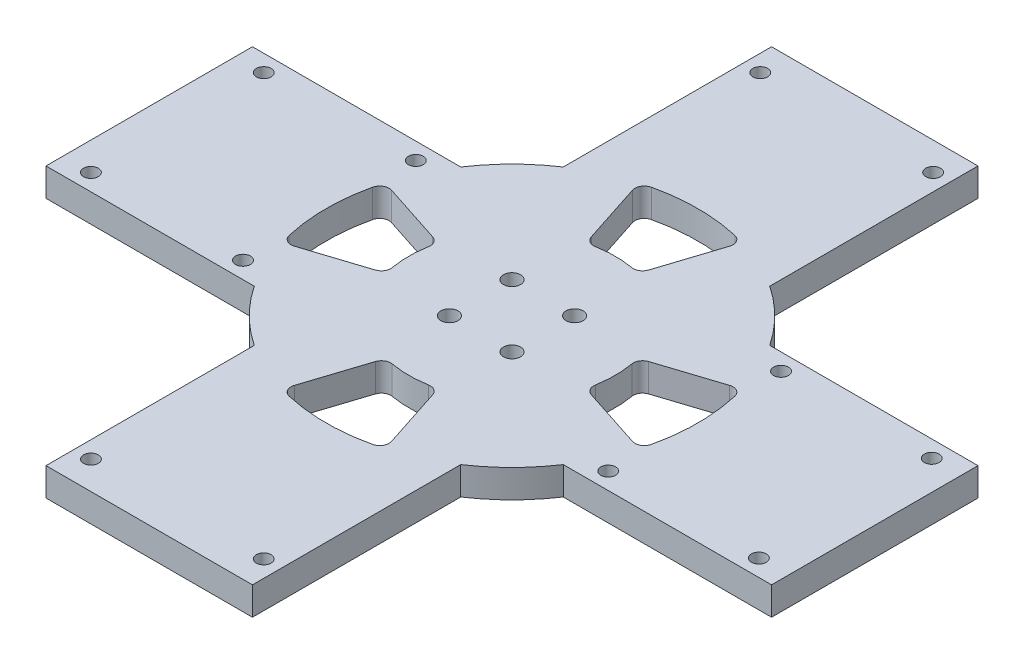
SolidWorks part; units mm, degrees
material "6061-T6 (SS)"
ref_plane "Front" through (0, 0, 0) normal (0, 0, 1) x (1, 0, 0)
ref_plane "Top" through (0, 0, 0) normal (0, 1, 0) x (1, 0, 0)
ref_plane "Right" through (0, 0, 0) normal (1, 0, 0) x (0, 0, -1)
sketch "Sketch1" plane through (0, 0, 0) normal (0, 1, 0) x (1, 0, 0)
  line L0 (0, 0) -> (8.8388, 8.8388) construction
  line L1 (0, 0) -> (-8.8388, -8.8388) construction
  line L2 (0, 0) -> (8.8388, -8.8388) construction
  line L3 (0, 0) -> (-8.8388, 8.8388) construction
  line L4 (-61.5, 17.5) -> (-26.1916, 17.5)
  line L5 (61.5, 17.5) -> (61.5, -17.5)
  line L6 (61.5, -17.5) -> (26.1916, -17.5)
  line L7 (-61.5, -17.5) -> (-61.5, 17.5)
  line L8 (-61.5, 0) -> (61.5, 0) construction
  line L9 (-17.5, 61.5) -> (17.5, 61.5)
  line L10 (-17.5, 61.5) -> (-17.5, 26.1916)
  line L11 (-17.5, -61.5) -> (17.5, -61.5)
  line L12 (17.5, -61.5) -> (17.5, -26.1916)
  line L13 (26.1916, 17.5) -> (61.5, 17.5)
  line L14 (-26.1916, -17.5) -> (-61.5, -17.5)
  line L15 (-17.5, -26.1916) -> (-17.5, -61.5)
  line L16 (17.5, 26.1916) -> (17.5, 61.5)
  line L17 (0, 61.5) -> (0, -61.5) construction
  line L18 (-8.75, 31.5) -> (-8.75, 15.1554) construction
  line L19 (8.75, 31.5) -> (8.75, 15.1554) construction
  line L20 (-31.5, 8.75) -> (-15.1554, 8.75) construction
  line L21 (-31.5, -8.75) -> (-15.1554, -8.75) construction
  line L22 (-8.75, -31.5) -> (-8.75, -15.1554) construction
  line L23 (8.75, -31.5) -> (8.75, -15.1554) construction
  line L24 (31.5, 8.75) -> (15.1554, 8.75) construction
  line L25 (31.5, -8.75) -> (15.1554, -8.75) construction
  line L34 (-4.4194, 4.4194) -> (-16.9328, 4.4194) construction
  line L35 (-4.4194, -4.4194) -> (-16.9328, -4.4194) construction
  line L36 (-4.4194, 4.4194) -> (-4.4194, 16.9328) construction
  line L37 (4.4194, 4.4194) -> (4.4194, 16.9328) construction
  line L38 (4.4194, 4.4194) -> (16.9328, 4.4194) construction
  line L39 (4.4194, -4.4194) -> (16.9328, -4.4194) construction
  line L40 (-4.4194, -4.4194) -> (-4.4194, -16.9328) construction
  line L41 (4.4194, -4.4194) -> (4.4194, -16.9328) construction
  line L42 (-18.3, 4.8637) -> (-28.6574, 8.2292)
  line L43 (-18.3, -4.8637) -> (-28.6574, -8.2292)
  line L44 (-4.8637, 18.3) -> (-8.2292, 28.6574)
  line L45 (4.8637, 18.3) -> (8.2292, 28.6574)
  line L46 (18.3, 4.8637) -> (28.6574, 8.2292)
  line L47 (18.3, -4.8637) -> (28.6574, -8.2292)
  line L48 (4.8637, -18.3) -> (8.2292, -28.6574)
  line L49 (-4.8637, -18.3) -> (-8.2292, -28.6574)
  arc A0 (-17.5, 26.1916) -> (-26.1916, 17.5) centre (0, 0) ccw
  arc A1 (26.1916, 17.5) -> (17.5, 26.1916) centre (0, 0) ccw
  arc A2 (17.5, -26.1916) -> (26.1916, -17.5) centre (0, 0) ccw
  arc A3 (-26.1916, -17.5) -> (-17.5, -26.1916) centre (0, 0) ccw
  arc A4 (-17.2277, 3.0749) -> (-17.2277, -3.0749) centre (0, 0) ccw
  arc A5 (-30.695, 7.076) -> (-30.695, -7.076) centre (0, 0) ccw
  arc A6 (7.076, 30.695) -> (-7.076, 30.695) centre (0, 0) ccw
  arc A7 (30.695, -7.076) -> (30.695, 7.076) centre (0, 0) ccw
  arc A8 (-7.076, -30.695) -> (7.076, -30.695) centre (0, 0) ccw
  arc A9 (3.0749, 17.2277) -> (-3.0749, 17.2277) centre (0, 0) ccw
  arc A10 (17.2277, -3.0749) -> (17.2277, 3.0749) centre (0, 0) ccw
  arc A11 (-3.0749, -17.2277) -> (3.0749, -17.2277) centre (0, 0) ccw
  arc A12 (8.2292, -28.6574) -> (7.076, -30.695) centre (6.7194, -29.148) cw
  arc A13 (-7.076, -30.695) -> (-8.2292, -28.6574) centre (-6.7194, -29.148) cw
  arc A14 (-4.8637, -18.3) -> (-3.0749, -17.2277) centre (-3.3539, -18.7905) cw
  arc A15 (3.0749, -17.2277) -> (4.8637, -18.3) centre (3.3539, -18.7905) cw
  arc A16 (28.6574, 8.2292) -> (30.695, 7.076) centre (29.148, 6.7194) cw
  arc A17 (30.695, -7.076) -> (28.6574, -8.2292) centre (29.148, -6.7194) cw
  arc A18 (18.3, -4.8637) -> (17.2277, -3.0749) centre (18.7905, -3.3539) cw
  arc A19 (17.2277, 3.0749) -> (18.3, 4.8637) centre (18.7905, 3.3539) cw
  arc A20 (-8.2292, 28.6574) -> (-7.076, 30.695) centre (-6.7194, 29.148) cw
  arc A21 (8.2292, 28.6574) -> (7.076, 30.695) centre (6.7194, 29.148) ccw
  arc A22 (4.8637, 18.3) -> (3.0749, 17.2277) centre (3.3539, 18.7905) cw
  arc A23 (-3.0749, 17.2277) -> (-4.8637, 18.3) centre (-3.3539, 18.7905) cw
  arc A24 (-18.3, 4.8637) -> (-17.2277, 3.0749) centre (-18.7905, 3.3539) cw
  arc A25 (-17.2277, -3.0749) -> (-18.3, -4.8637) centre (-18.7905, -3.3539) cw
  arc A26 (-28.6574, -8.2292) -> (-30.695, -7.076) centre (-29.148, -6.7194) cw
  arc A27 (-28.6574, 8.2292) -> (-30.695, 7.076) centre (-29.148, 6.7194) ccw
  circle A28 centre (0, 0) radius 6.25 construction
  point P7 (-31.5, 0)
  point P8 (36.1916, -17.5)
  point P9 (0, 31.5)
  point P10 (31.5, 0)
  point P11 (36.1916, 17.5)
  point P12 (-36.1916, -17.5)
  point P14 (-61.5, 17.5)
  point P15 (-61.5, -17.5)
  point P16 (61.5, 17.5)
  point P17 (61.5, -17.5)
  point P20 (-51.5, 17.5)
  point P23 (-51.5, -17.5)
  point P24 (51.5, 17.5)
  point P25 (51.5, -17.5)
  point P27 (61.5, 0)
  point P28 (-61.5, 0)
  point P32 (0, -31.5)
  point P33 (0, -31.5)
  point P35 (-36.1916, 17.5)
  point P38 (0, 61.5)
  point P39 (4.4194, 4.4194)
  point P44 (-8.75, 31.5)
  point P45 (8.75, 31.5)
  point P57 (-31.5, 8.75)
  point P58 (-31.5, -8.75)
  point P63 (31.5, 8.75)
  point P64 (31.5, -8.75)
  point P65 (8.75, -31.5)
  point P66 (-8.75, -31.5)
  point P83 (-4.4194, 4.4194)
  point P84 (-4.4194, -4.4194)
  point P85 (4.4194, -4.4194)
  point P100 (8.75, -30.2603)
  point P103 (-8.75, -30.2603)
  point P112 (30.2603, 8.75)
  point P115 (30.2603, -8.75)
  point P124 (-8.75, 30.2603)
  point P127 (8.75, 30.2603)
  point P142 (-30.2603, -8.75)
  point P145 (-30.2603, 8.75)
  dimension "D1" = 10
  dimension "D3" = 30
  dimension "D9" = 17.5
  dimension "D17" = 1.5875
  dimension "D2" = 10
  dimension "D4" = 10
  dimension "D5" = 10
  dimension "D6" = 30
  dimension "D7" = 30
  dimension "D8" = 30
  dimension "D10" = 8.75
  dimension "D11" = 17.5
  dimension "D12" = 8.75
  dimension "D13" = 17.5
  dimension "D14" = 8.75
  dimension "D15" = 17.5
  dimension "D16" = 8.75
extrude "Boss-Extrude1" add sketch "Sketch1" along normal blind 4.763
hole_wizard "M2.5 Clearance Hole1" positions "Sketch3" profile "Sketch2" hole size "M2.5" standard "ANSI Metric" end condition through all
sketch "Sketch3" plane through (0, 4.763, 0) normal (0, 1, 0) x (1, 0, 0)
  line L0 (0, 0) -> (5.3033, 5.3033) construction
  line L2 (0, 0) -> (-5.3033, 5.3033) construction
  line L4 (0, 0) -> (-5.3033, -5.3033) construction
  line L6 (0, 0) -> (5.3033, -5.3033) construction
  point P2 (5.3033, 5.3033)
  point P8 (-5.3033, 5.3033)
  point P11 (-5.3033, -5.3033)
  point P16 (5.3033, -5.3033)
sketch "Sketch2" plane through (5.3033, 4.763, -5.3033) normal (1, 0, 0) x (0, 0, 1)
  line L0 (0, 0) -> (0, 4.763)
  line L1 (0, 4.763) -> (1.45, 4.763)
  line L2 (1.45, 4.763) -> (1.45, 0)
  line L5 (1.45, 0) -> (0, 0)
  line L11 (0, -6.35) -> (0, 107.95) construction
  dimension "Thru Hole Dia." = 2.9
  dimension "Thru Hole Depth" = 4.763
hole_wizard "Tap Drill for M3x0.5 Tap1" positions "Sketch5" profile "Sketch4" hole size "M3x0.5" standard "ANSI Metric" end condition up to next
sketch "Sketch5" plane through (0, 4.763, 0) normal (0, 1, 0) x (1, 0, 0)
  line L0 (-51.975, 17.5) -> (-51.975, -17.5) construction
  line L1 (-26.1916, 17.5) -> (-61.5, 17.5) construction
  line L2 (-61.5, -17.5) -> (-26.1916, -17.5) construction
  line L4 (-61.5, 17.5) -> (-61.5, -17.5) construction
  line L5 (-35.7166, 17.5) -> (-35.7166, -17.5) construction
  line L7 (-26.1916, 17.5) -> (-26.1916, -17.5) construction
  line L9 (26.1916, 17.5) -> (26.1916, -17.5) construction
  line L11 (35.7166, 17.5) -> (35.7166, -17.5) construction
  line L12 (61.5, 17.5) -> (26.1916, 17.5) construction
  line L13 (26.1916, -17.5) -> (61.5, -17.5) construction
  line L15 (51.975, 17.5) -> (51.975, -17.5) construction
  line L17 (61.5, -17.5) -> (61.5, 17.5) construction
  line L18 (-17.5, 51.975) -> (17.5, 51.975) construction
  line L19 (-17.5, 61.5) -> (-17.5, 26.1916) construction
  line L20 (17.5, 26.1916) -> (17.5, 61.5) construction
  line L22 (17.5, 61.5) -> (-17.5, 61.5) construction
  line L23 (-17.5, -51.975) -> (17.5, -51.975) construction
  line L24 (-17.5, -26.1916) -> (-17.5, -61.5) construction
  line L25 (17.5, -61.5) -> (17.5, -26.1916) construction
  line L27 (-17.5, -61.5) -> (17.5, -61.5) construction
  point P0 (-56.7375, 14.65)
  point P42 (-30.9541, 14.65)
  point P51 (-56.7375, -14.65)
  point P55 (30.9541, 14.65)
  point P57 (56.5, 14.65)
  point P59 (-30.9541, -14.65)
  point P61 (30.9541, -14.65)
  point P63 (56.5, -14.65)
  point P87 (0, -61.5)
  point P90 (-14.65, 56.7375)
  point P92 (14.65, 56.7375)
  point P107 (-14.65, -56.7375)
  point P109 (14.65, -56.7375)
  dimension "D1" = 9.525
  dimension "D2" = 9.525
  dimension "D3" = 9.525
  dimension "D4" = 9.525
  dimension "D5" = 2.85
  dimension "D6" = 4.7625
  dimension "D7" = 2.85
  dimension "D8" = 4.7625
  dimension "D9" = 4.7625
  dimension "D10" = 5
  dimension "D11" = 9.525
  dimension "D12" = 9.525
  dimension "D13" = 2.85
  dimension "D14" = 4.7625
  dimension "D15" = 2.85
  dimension "D16" = 4.7625
sketch "Sketch4" plane through (-56.7375, 4.763, -14.65) normal (1, 0, 0) x (0, 0, 1)
  line L0 (0, 0) -> (0, 4.763)
  line L1 (0, 4.763) -> (1.25, 4.763)
  line L2 (1.25, 4.763) -> (1.25, 0)
  line L5 (1.25, 0) -> (0, 0)
  line L11 (0, -6.35) -> (0, 107.95) construction
  dimension "Thru Hole Dia." = 2.5
  dimension "Thru Hole Depth" = 4.763
